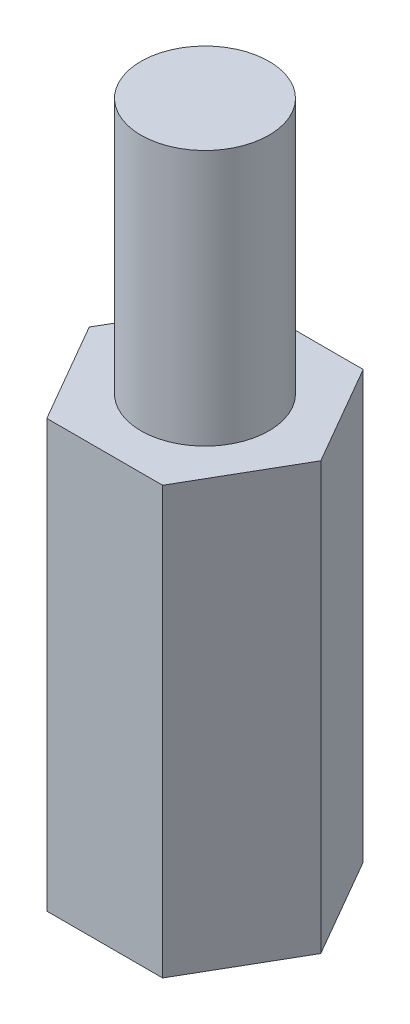
SolidWorks part; units mm, degrees
ref_plane "Front Plane" through (0, 0, 0) normal (0, 0, 1) x (1, 0, 0)
ref_plane "Top Plane" through (0, 0, 0) normal (0, 1, 0) x (1, 0, 0)
ref_plane "Right Plane" through (0, 0, 0) normal (1, 0, 0) x (0, 0, -1)
sketch "Sketch1" plane through (0, 0, 0) normal (0, 1, 0) x (1, 0, 0)
  line L0 (0, 0) -> (2.7135, 0) construction
  line L1 (2.7135, 0) -> (1.3568, 2.35)
  line L2 (1.3568, 2.35) -> (-1.3568, 2.35)
  line L3 (-1.3568, 2.35) -> (-2.7135, 0)
  line L4 (-2.7135, 0) -> (-1.3568, -2.35)
  line L5 (-1.3568, -2.35) -> (1.3568, -2.35)
  line L6 (1.3568, -2.35) -> (2.7135, 0)
  circle A0 centre (0, 0) radius 2.35 construction
  dimension "D1" = 4.7
extrude "Boss-Extrude1" add sketch "Sketch1" along normal blind 10
sketch "Sketch2" plane through (0, 10, 0) normal (0, 1, 0) x (1, 0, 0)
  circle A0 centre (0, 0) radius 1.5
  dimension "D1" = 3
extrude "Boss-Extrude2" add sketch "Sketch2" along normal blind 6
sketch "Sketch3" plane through (0, 0, 0) normal (0, -1, 0) x (1, 0, 0)
  circle A0 centre (0, 0) radius 1.25
  dimension "D1" = 2.5
extrude "Cut-Extrude1" cut sketch "Sketch3" against normal blind 6
